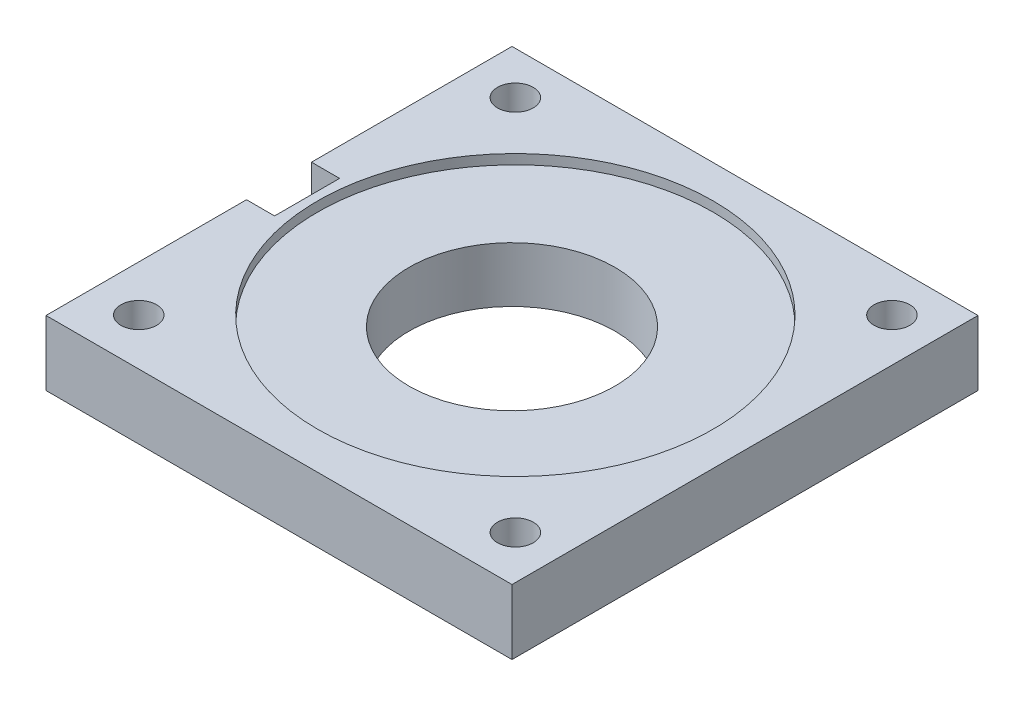
SolidWorks part; units mm, degrees
ref_plane "Front Plane" through (0, 0, 0) normal (0, 0, 1) x (1, 0, 0)
ref_plane "Top Plane" through (0, 0, 0) normal (0, 1, 0) x (1, 0, 0)
ref_plane "Right Plane" through (0, 0, 0) normal (1, 0, 0) x (0, 0, -1)
sketch "Sketch1" plane through (0, 0, 0) normal (0, 1, 0) x (1, 0, 0)
  line L1 (-43, 43) -> (43, 43)
  line L2 (-43, 43) -> (-43, -43)
  line L3 (-43, -43) -> (43, -43)
  line L4 (43, 43) -> (43, -43)
  line L5 (-43, 43) -> (43, -43) construction
  line L6 (-43, -43) -> (43, 43) construction
  circle A0 centre (0, 0) radius 19
  point P0 (0, 0)
  dimension "D3" = 38
  dimension "D1" = 86
  dimension "D2" = 86
extrude "Boss-Extrude1" add sketch "Sketch1" along normal blind 12
sketch "Sketch2" plane through (0, 12, 0) normal (0, 1, 0) x (1, 0, 0)
  circle A0 centre (-34.5076, -34.3733) radius 3.3 construction
  circle A1 centre (-34.5076, 35.1267) radius 3.3 construction
  circle A2 centre (34.9924, -34.3733) radius 3.3 construction
  circle A3 centre (34.9924, 35.1267) radius 3.3 construction
  circle A4 centre (-34.5076, -34.3733) radius 3.3
  circle A5 centre (-34.5076, 35.1267) radius 3.3
  circle A6 centre (34.9924, -34.3733) radius 3.3
  circle A7 centre (34.9924, 35.1267) radius 3.3
extrude "Cut-Extrude1" cut sketch "Sketch2" against normal up to next
sketch "Sketch4" plane through (0, 12, 0) normal (0, 1, 0) x (1, 0, 0)
  circle A0 centre (0.2424, 0.3767) radius 36.5
  dimension "D1" = 73
extrude "Cut-Extrude2" cut sketch "Sketch4" against normal blind 1.8
sketch "Sketch6" plane through (0, 12, 0) normal (0, 1, 0) x (1, 0, 0)
  line L0 (0, 0) -> (-70.5299, 0) construction
  line L2 (-45.887, 6) -> (-37.8164, 6)
  line L3 (-45.887, 6) -> (-45.887, -6)
  line L4 (-45.887, -6) -> (-37.8164, -6)
  line L5 (-37.8164, 6) -> (-37.8164, -6)
  line L6 (-45.887, 6) -> (-37.8164, -6) construction
  line L7 (-45.887, -6) -> (-37.8164, 6) construction
  point P3 (-41.8517, 0)
  dimension "D1" = 12
extrude "Cut-Extrude3" cut sketch "Sketch6" against normal through all
